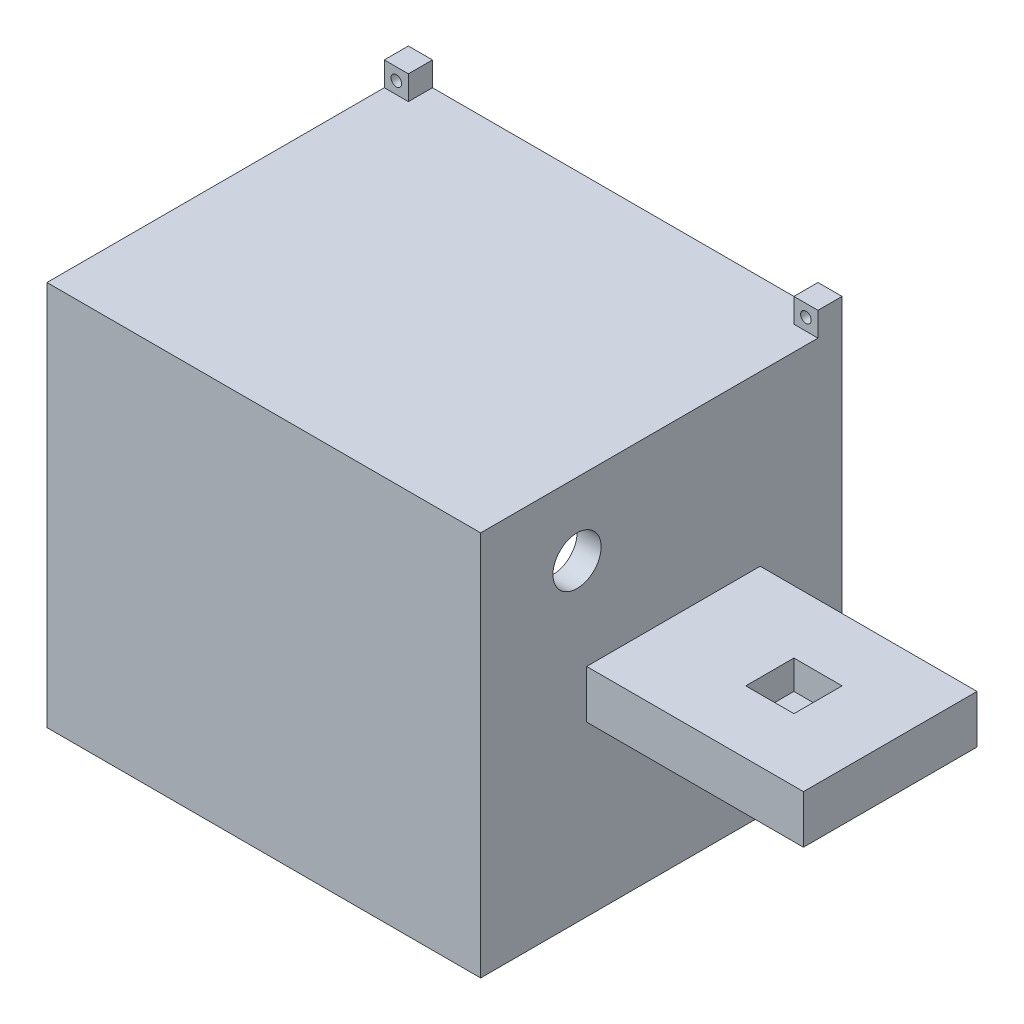
SolidWorks part; units mm, degrees
ref_plane "前基準面" through (0, 0, 0) normal (0, 0, 1) x (1, 0, 0)
ref_plane "上基準面" through (0, 0, 0) normal (0, 1, 0) x (1, 0, 0)
ref_plane "右基準面" through (0, 0, 0) normal (1, 0, 0) x (0, 0, -1)
sketch "草圖1" plane through (0, 0, 0) normal (0, 0, 1) x (1, 0, 0)
  line L0 (-75.5089, 45.5899) -> (59.4911, 45.5899)
  line L4 (-75.5089, 5.5899) -> (59.4911, 5.5899) construction
  line L5 (-75.5089, 45.5899) -> (-75.5089, -34.4101)
  line L6 (59.4911, 45.5899) -> (59.4911, -34.4101)
  line L7 (-75.5089, -34.4101) -> (59.4911, -34.4101)
  dimension "D1" = 135
  dimension "D2" = 80
extrude "填料-伸長1" add sketch "草圖1" along normal blind 70
sketch "草圖5" plane through (0, -34.4101, 0) normal (0, -1, 0) x (1, 0, 0)
  line L0 (14.4911, 70) -> (14.4911, 0)
  line L1 (-75.5089, 70) -> (59.4911, 70) construction
  line L2 (-75.5089, 0) -> (59.4911, 0) construction
  line L3 (14.4911, 0) -> (59.4911, 0)
  line L4 (59.4911, 0) -> (59.4911, 70)
  line L5 (59.4911, 70) -> (14.4911, 70)
  dimension "D1" = 45
sketch "草圖6" plane through (0, 45.5899, 0) normal (0, 1, 0) x (1, 0, 0)
  line L0 (14.4911, 0) -> (14.4911, -70)
  line L1 (14.4911, -70) -> (59.4911, -70)
  line L2 (59.4911, -70) -> (59.4911, 0)
  line L3 (59.4911, 0) -> (14.4911, 0)
extrude "除料-伸長1" cut sketch "草圖6" against normal blind 35
extrude "除料-伸長2" cut sketch "草圖5" against normal blind 35
sketch "草圖7" plane through (0, 0, 0) normal (0, 0, 1) x (1, 0, 0)
  line L0 (-75.5089, 5.5899) -> (59.4911, 5.5899) construction
  line L1 (-75.5089, 45.5899) -> (-75.5089, -34.4101) construction
  line L2 (59.4911, 0.5899) -> (59.4911, 10.5899) construction
  line L3 (-70.5089, -29.4101) -> (-70.5089, 40.5899)
  line L4 (-70.5089, 40.5899) -> (9.4911, 40.5899)
  line L5 (9.4911, 40.5899) -> (9.4911, -29.4101)
  line L6 (-70.5089, -29.4101) -> (9.4911, -29.4101)
  line L7 (14.4911, 45.5899) -> (-75.5089, 45.5899) construction
  line L8 (14.4911, 0.5899) -> (14.4911, -34.4101) construction
  point P11 (9.4911, 5.5899)
  point P12 (-70.5089, 5.5899)
  dimension "D1" = 5
  dimension "D2" = 5
  dimension "D3" = 5
extrude "除料-伸長3" cut sketch "草圖7" along normal blind 75
sketch "草圖8" plane through (0, 0, 0) normal (0, 0, -1) x (-1, 0, 0)
  line L0 (-59.4911, 5.5899) -> (75.5089, 5.5899) construction
  line L1 (-59.4911, 0.5899) -> (-59.4911, 10.5899) construction
  line L2 (75.5089, 45.5899) -> (75.5089, -34.4101) construction
  line L3 (-13.3911, 44.4899) -> (-13.3911, -33.3101)
  line L4 (-13.3911, 44.4899) -> (74.4089, 44.4899)
  line L5 (74.4089, 44.4899) -> (74.4089, -33.3101)
  line L7 (71.6089, -30.5101) -> (71.6089, 41.6899)
  line L8 (71.6089, 41.6899) -> (-10.5911, 41.6899)
  line L9 (-10.5911, 41.6899) -> (-10.5911, -30.5101)
  line L11 (-14.4911, 45.5899) -> (75.5089, 45.5899) construction
  line L12 (-14.4911, 10.5899) -> (-14.4911, 45.5899) construction
  line L13 (71.6089, -30.5101) -> (-10.5911, -30.5101)
  line L14 (-13.3911, -33.3101) -> (74.4089, -33.3101)
  dimension "D1" = 2.8
  dimension "D2" = 2.8
  dimension "D3" = 2.8
  dimension "D4" = 1.1
  dimension "D5" = 1.1
  dimension "D6" = 1.1
extrude "除料-伸長4" cut sketch "草圖8" against normal blind 10
ref_plane "平面1" through (14.4911, 0, 0) normal (1, 0, 0) x (0, 0, -1)
sketch "草圖9" plane through (14.4911, 0, 0) normal (1, 0, 0) x (0, 0, -1)
  line L0 (-70, 5.5899) -> (0, 5.5899) construction
  line L1 (-70, 0.5899) -> (-70, 10.5899) construction
  line L2 (0, 0.5899) -> (0, 10.5899) construction
  line L3 (0, 41.6899) -> (0, -30.5101) construction
  line L4 (-70, 10.5899) -> (-70, 45.5899) construction
  line L5 (0, 10.5899) -> (-70, 10.5899) construction
  line L6 (0, 0.5899) -> (-70, 0.5899) construction
  circle A2 centre (-55, 30.5899) radius 5
  circle A3 centre (-20, -19.4101) radius 5
  dimension "D1" = 10
  dimension "D2" = 10
  dimension "D3" = 20
  dimension "D4" = 15
  dimension "D5" = 20
  dimension "D6" = 20
extrude "除料-伸長5" cut sketch "草圖9" against normal blind 32.4
ref_plane "平面2" through (0, -34.4101, 0) normal (0, -1, 0) x (-1, 0, 0)
sketch "草圖10" plane through (0, -34.4101, 0) normal (0, -1, 0) x (-1, 0, 0)
  line L0 (75.5089, 0) -> (-14.4911, 0) construction
  line L1 (14.0089, -11) -> (35.5089, -11)
  line L2 (14.0089, -11) -> (14.0089, -26)
  line L3 (14.0089, -26) -> (35.5089, -26)
  line L4 (35.5089, -11) -> (35.5089, -26)
  line L5 (75.5089, -70) -> (75.5089, 0) construction
  point P6 (24.7589, -11)
  dimension "D1" = 21.5
  dimension "D2" = 15
  dimension "D3" = 11
  dimension "D4" = 40
extrude "除料-伸長6" cut sketch "草圖10" against normal blind 10
sketch "草圖12" plane through (14.4911, 0, 0) normal (1, 0, 0) x (0, 0, -1)
  line L0 (-35, 45.5899) -> (-35, -34.4101) construction
  line L1 (0, 45.5899) -> (-70, 45.5899) construction
  line L2 (-70, -34.4101) -> (0, -34.4101) construction
  line L3 (-70, 10.5899) -> (-70, 0.5899)
  line L4 (-70, 0.5899) -> (-53.0093, 0.5899)
  line L5 (0, 0.5899) -> (-70, 0.5899) construction
  line L6 (-53.0093, 0.5899) -> (-53.0093, 10.5899)
  line L7 (0, 10.5899) -> (-70, 10.5899) construction
  line L8 (-53.0093, 10.5899) -> (-70, 10.5899)
  line L9 (-16.9907, 10.5899) -> (0, 10.5899)
  line L10 (0, 10.5899) -> (0, 0.5899)
  line L11 (0, 0.5899) -> (-16.9907, 0.5899)
  line L12 (-16.9907, 0.5899) -> (-16.9907, 10.5899)
extrude "除料-伸長7" cut sketch "草圖12" along normal blind 45
ref_plane "平面3" through (0, 0.5899, 0) normal (0, -1, 0) x (-1, 0, 0)
sketch "草圖14" plane through (0, 0.5899, 0) normal (0, -1, 0) x (-1, 0, 0)
  line L4 (-59.4911, -35) -> (-70.9929, -35) construction
  line L5 (-59.4911, -16.9907) -> (-59.4911, -53.0093) construction
  line L6 (-38.0091, -30.1028) -> (-21.5179, -33.5)
  line L7 (-38.0091, -39.8972) -> (-21.5179, -36.5)
  line L8 (-39.0179, -40) -> (-39.0179, -45.1799) construction
  line L9 (-40.0267, -39.8972) -> (-56.5179, -36.5)
  line L10 (-40.0267, -30.1028) -> (-56.5179, -33.5)
  line L11 (-49.9929, -35) -> (-38.9929, -35) construction
  line L12 (-20.0179, -35) -> (-28.4331, -35) construction
  arc A2 (-40.0267, -39.8972) -> (-38.0091, -39.8972) centre (-39.0179, -35) ccw
  arc A3 (-21.5179, -36.5) -> (-21.5179, -33.5) centre (-21.5179, -35) ccw
  arc A5 (-56.5179, -36.5) -> (-56.5179, -33.5) centre (-56.5179, -35) cw
  arc A6 (-38.0091, -30.1028) -> (-40.0267, -30.1028) centre (-39.0179, -35) ccw
  dimension "D1" = 10
  dimension "D2" = 3
extrude "除料-伸長8" cut sketch "草圖14" against normal blind 3
ref_plane "平面4" through (0, 10.5899, 0) normal (0, 1, 0) x (1, 0, 0)
sketch "草圖15" plane through (0, 10.5899, 0) normal (0, 1, 0) x (1, 0, 0)
  line L0 (14.4911, -16.9907) -> (14.4911, -53.0093) construction
  line L1 (34.4911, -29.9907) -> (44.4911, -29.9907)
  line L2 (34.4911, -29.9907) -> (34.4911, -39.9907)
  line L3 (34.4911, -39.9907) -> (44.4911, -39.9907)
  line L4 (44.4911, -29.9907) -> (44.4911, -39.9907)
  line L5 (59.4911, -16.9907) -> (14.4911, -16.9907) construction
  dimension "D1" = 10
  dimension "D2" = 10
  dimension "D3" = 20
  dimension "D4" = 13
extrude "除料-伸長9" cut sketch "草圖15" against normal blind 6
sketch "草圖17" plane through (0, 0.5899, 0) normal (0, -1, 0) x (-1, 0, 0)
  line L0 (-58.0179, -35) -> (-20.0179, -35) construction
  line L1 (-39.0179, -40) -> (-39.0179, -30) construction
  arc A0 (-56.5179, -33.5) -> (-56.5179, -36.5) centre (-56.5179, -35) ccw construction
  arc A1 (-21.5179, -36.5) -> (-21.5179, -33.5) centre (-21.5179, -35) ccw construction
  arc A2 (-40.0267, -39.8972) -> (-38.0091, -39.8972) centre (-39.0179, -35) ccw construction
  arc A3 (-38.0091, -30.1028) -> (-40.0267, -30.1028) centre (-39.0179, -35) ccw construction
  circle A4 centre (-39.0179, -35) radius 1.0953
extrude "除料-伸長11" cut sketch "草圖17" against normal blind 7
sketch "草圖18" plane through (0, 0, 0) normal (0, 0, 1) x (1, 0, 0)
  line L0 (59.4911, 5.5899) -> (-75.5089, 5.5899) construction
  line L1 (59.4911, 10.5899) -> (59.4911, 0.5899) construction
  line L2 (-75.5089, 45.5899) -> (-75.5089, -34.4101) construction
  line L3 (14.4911, 45.5899) -> (-75.5089, 45.5899) construction
  line L4 (-30.5089, 45.5899) -> (-30.5089, -34.4101) construction
  line L5 (-38.5, -34.4101) -> (38.5, -34.4101) construction
  line L6 (14.4911, -43.147) -> (14.4911, 43.147) construction
  line L7 (14.4911, 45.5899) -> (9.4911, 45.5899)
  line L8 (14.4911, 45.5899) -> (14.4911, 50.5899)
  line L9 (14.4911, 50.5899) -> (9.4911, 50.5899)
  line L10 (9.4911, 45.5899) -> (9.4911, 50.5899)
  line L11 (14.4911, 48.0899) -> (9.4911, 48.0899) construction
  line L12 (11.9911, 50.5899) -> (11.9911, 45.5899) construction
  line L13 (-75.5089, 50.5899) -> (-70.5089, 50.5899)
  line L14 (-70.5089, 45.5899) -> (-70.5089, 50.5899)
  line L15 (-75.5089, 45.5899) -> (-70.5089, 45.5899)
  line L16 (-75.5089, 45.5899) -> (-75.5089, 50.5899)
  line L17 (-75.5089, -34.4101) -> (-70.5089, -34.4101)
  line L18 (-75.5089, -34.4101) -> (-75.5089, -39.4101)
  line L19 (-75.5089, -39.4101) -> (-70.5089, -39.4101)
  line L20 (-70.5089, -34.4101) -> (-70.5089, -39.4101)
  line L21 (14.4911, -34.4101) -> (9.4911, -34.4101)
  line L22 (9.4911, -34.4101) -> (9.4911, -39.4101)
  line L23 (14.4911, -39.4101) -> (9.4911, -39.4101)
  line L24 (14.4911, -34.4101) -> (14.4911, -39.4101)
  circle A0 centre (11.9911, 48.0899) radius 1.1
  circle A1 centre (-73.0089, 48.0899) radius 1.1
  circle A2 centre (-73.0089, -36.9101) radius 1.1
  circle A3 centre (11.9911, -36.9101) radius 1.1
  dimension "D3" = 2.2
  dimension "D1" = 5
  dimension "D2" = 5
extrude "填料-伸長2" add sketch "草圖18" along normal blind 5
ref_plane "平面5" through (0, 0, 70) normal (0, 0, 1) x (1, 0, 0)
sketch "草圖19" plane through (0, 0, 70) normal (0, 0, 1) x (1, 0, 0)
  line L0 (14.4911, -43.147) -> (14.4911, 43.147) construction
  line L1 (-75.5089, 45.5899) -> (14.4911, 45.5899)
  line L2 (-75.5089, 45.5899) -> (-75.5089, -34.4101)
  line L3 (-75.5089, -34.4101) -> (14.4911, -34.4101)
  line L4 (14.4911, 45.5899) -> (14.4911, -34.4101)
  dimension "D1" = 80
  dimension "D2" = 90
extrude "填料-伸長3" add sketch "草圖19" along normal blind 5
